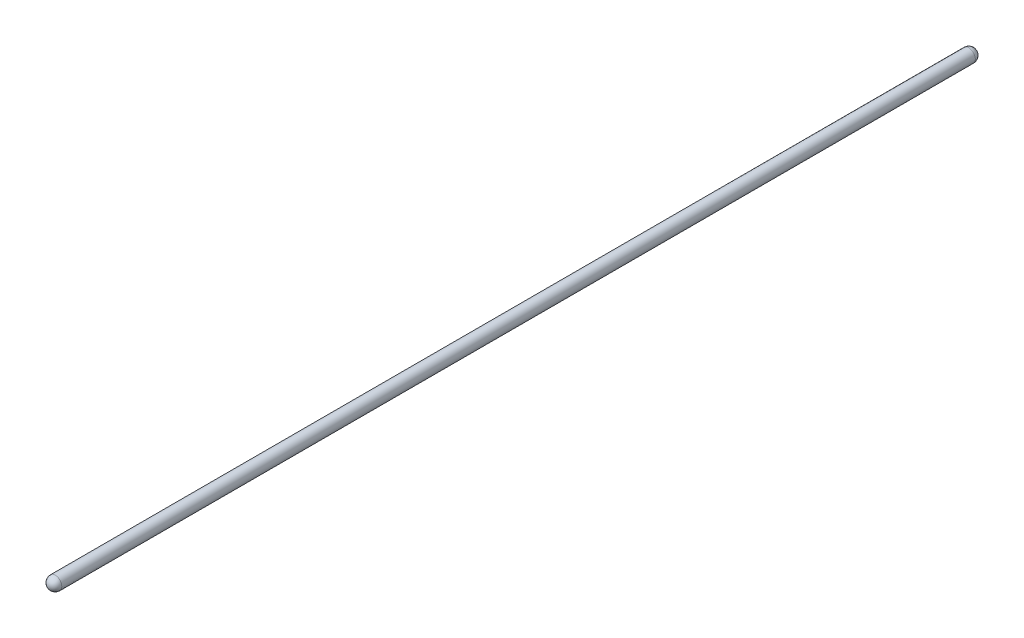
SolidWorks part; units mm, degrees
ref_plane "Front Plane" through (0, 0, 0) normal (0, 0, 1) x (1, 0, 0)
ref_plane "Top Plane" through (0, 0, 0) normal (0, 1, 0) x (1, 0, 0)
ref_plane "Right Plane" through (0, 0, 0) normal (1, 0, 0) x (0, 0, -1)
sketch "Sketch1" plane through (0, 0, 0) normal (0, 1, 0) x (1, 0, 0)
  line L0 (0, 0) -> (0, 9.525) construction
  line L1 (0, 0) -> (9.525, 0) construction
  line L2 (0, 0) -> (0, -1327.7698) construction
  line L3 (0, -1327.7698) -> (9.525, -1327.7698) construction
  line L4 (0, -1327.7698) -> (0, -1337.2948) construction
  line L5 (9.525, 0) -> (9.525, -1327.7698)
  line L6 (0, 9.525) -> (0, -1337.2948)
  arc A1 (0, 9.525) -> (9.525, 0) centre (0, 0) cw
  arc A2 (9.525, -1327.7698) -> (0, -1337.2948) centre (0, -1327.7698) cw
revolve "Revolve1" add sketch "Sketch1" angle 360 about L6
